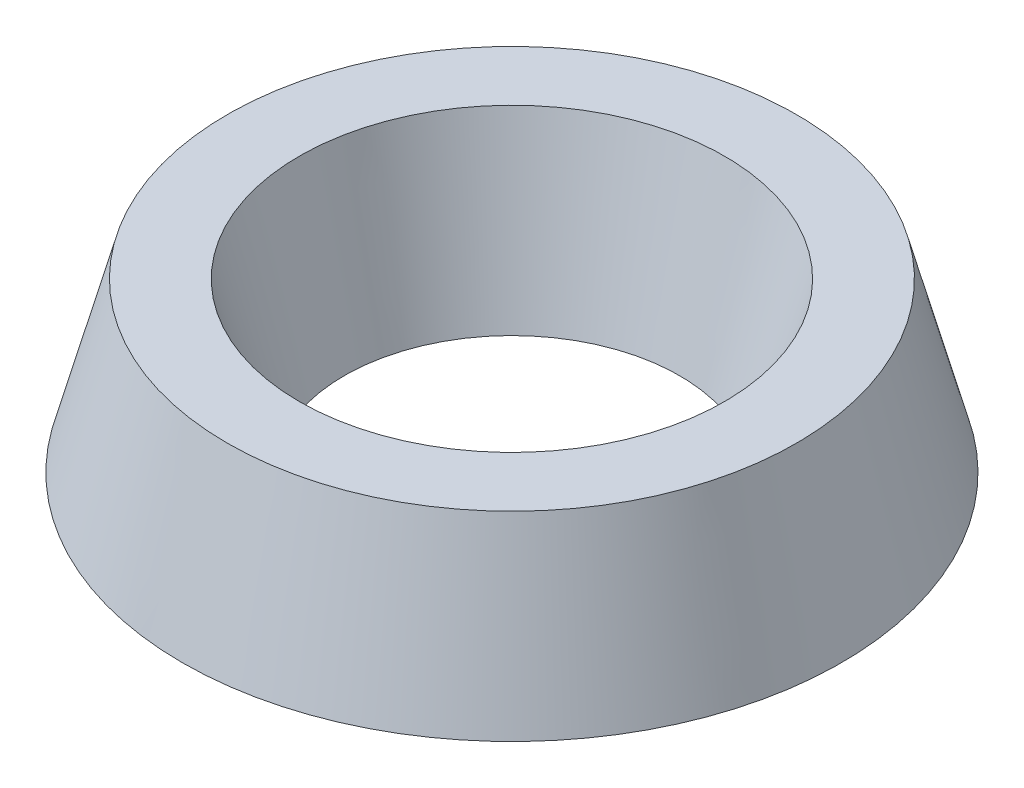
SolidWorks part; units mm, degrees
material "Chrome Stainless Steel"
ref_plane "Front Plane" through (0, 0, 0) normal (0, 0, 1) x (1, 0, 0)
ref_plane "Top Plane" through (0, 0, 0) normal (0, 1, 0) x (1, 0, 0)
ref_plane "Right Plane" through (0, 0, 0) normal (1, 0, 0) x (0, 0, -1)
sketch "Sketch1" plane through (0, 0, 0) normal (0, 1, 0) x (1, 0, 0)
  circle A0 centre (0, 0) radius 3
  circle A1 centre (0, 0) radius 5.8961
  dimension "D1" = 6
extrude "Boss-Extrude1" add sketch "Sketch1" along normal blind 3 draft 15
